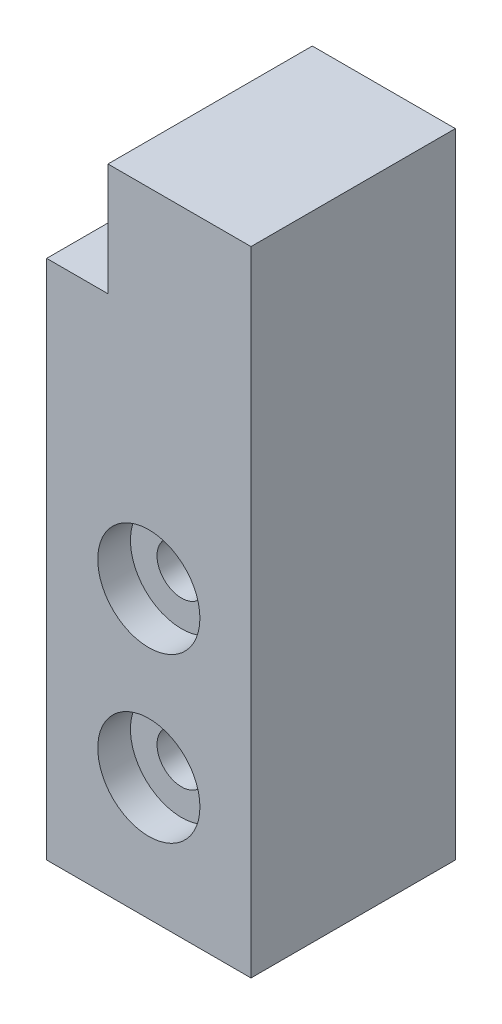
SolidWorks part; units mm, degrees
ref_plane "正面" through (0, 0, 0) normal (0, 0, 1) x (1, 0, 0)
ref_plane "平面" through (0, 0, 0) normal (0, 1, 0) x (1, 0, 0)
ref_plane "右側面" through (0, 0, 0) normal (1, 0, 0) x (0, 0, -1)
sketch "Sketch1" plane through (0, 0, 0) normal (0, 0, 1) x (1, 0, 0)
  line L1 (0, 0) -> (10, 0)
  line L2 (0, 0) -> (0, 31)
  line L3 (0, 31) -> (10, 31)
  line L4 (10, 0) -> (10, 31)
extrude "Boss-Extrude1" add sketch "Sketch1" along normal blind 10
sketch "Sketch2" plane through (0, 0, 10) normal (0, 0, 1) x (1, 0, 0)
  line L5 (0, 31) -> (3, 31)
  line L6 (0, 31) -> (0, 25.5)
  line L7 (0, 25.5) -> (3, 25.5)
  line L8 (3, 31) -> (3, 25.5)
extrude "Cut-Extrude1" cut sketch "Sketch2" against normal blind 10
hole_wizard "CBORE for M2 Pan Head Screw1" positions "Sketch3" profile "Sketch4" counterbore size "M2" standard "JIS"
sketch "Sketch3" plane through (0, 0, 10) normal (0, 0, 1) x (1, 0, 0)
  line L1 (0, 25.5) -> (0, 0) construction
  line L2 (0, 0) -> (10, 0) construction
  point P0 (5, 14)
  point P2 (5, 6)
  dimension "D1" = 5
  dimension "D2" = 5
  dimension "D3" = 6
  dimension "D4" = 14
sketch "Sketch4" plane through (5, 14, 10) normal (1, 0, 0) x (0, -1, 0)
  line L0 (0, 0) -> (0, 10.721)
  line L1 (0, 10.721) -> (1.2, 10)
  line L2 (1.2, 10) -> (1.2, 1.6)
  line L3 (1.2, 1.6) -> (2.5, 1.6)
  line L4 (2.5, 1.6) -> (2.5, 0)
  line L5 (2.5, 0) -> (0, 0)
  line L10 (0, 10.721) -> (-1.2, 10) construction
  line L11 (0, -6.35) -> (0, 107.95) construction
  dimension "Hole Dia." = 2.4
  dimension "Hole Depth" = 10
  dimension "C'Bore Dia." = 5
  dimension "C'Bore Depth" = 1.6
  dimension "Drill Angle" = 118
